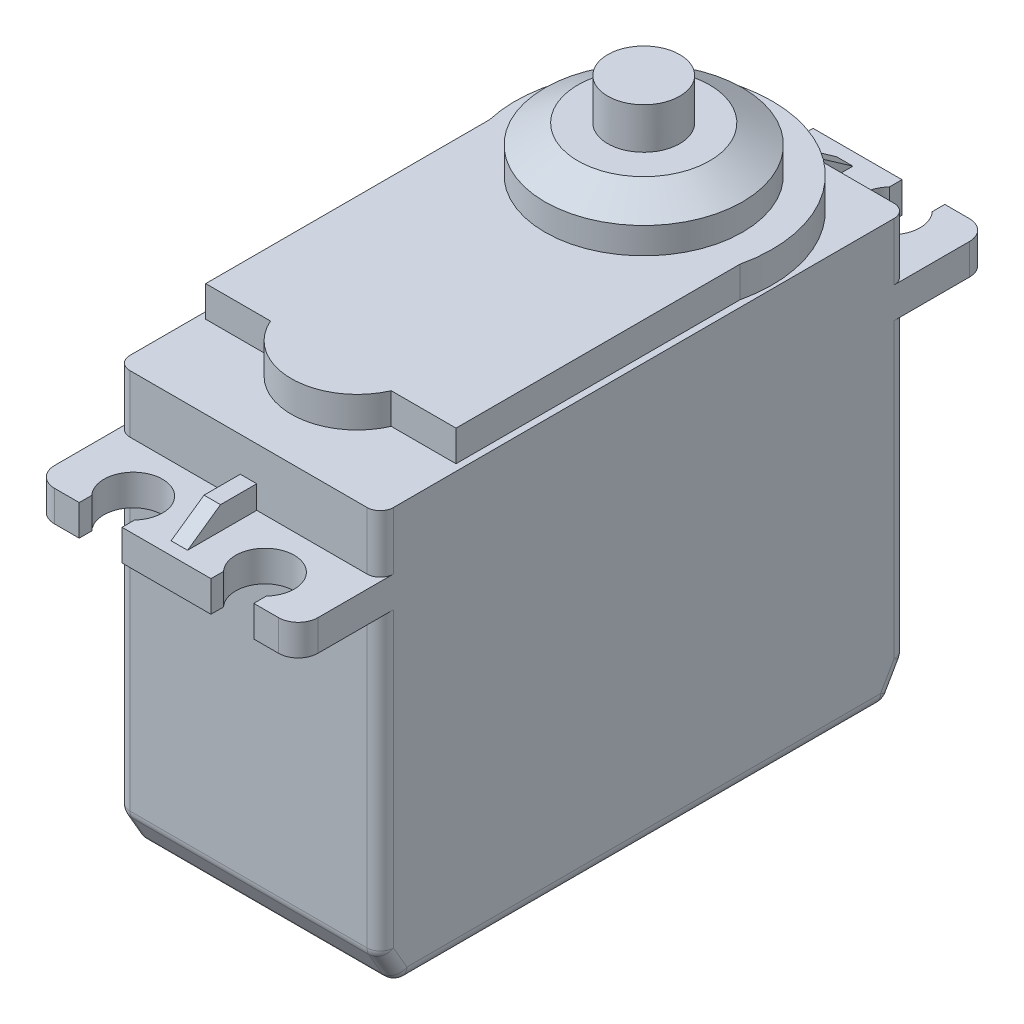
SolidWorks part; units mm, degrees
ref_plane "Front Plane" through (0, 0, 0) normal (0, 0, 1) x (1, 0, 0)
ref_plane "Top Plane" through (0, 0, 0) normal (0, 1, 0) x (1, 0, 0)
ref_plane "Right Plane" through (0, 0, 0) normal (1, 0, 0) x (0, 0, -1)
sketch "Sketch1" plane through (0, 0, 0) normal (0, 1, 0) x (1, 0, 0)
  line L1 (-10.16, 10.16) -> (10.16, 10.16)
  line L2 (-10.16, 10.16) -> (-10.16, -30.48)
  line L3 (-10.16, -30.48) -> (10.16, -30.48)
  line L4 (10.16, 10.16) -> (10.16, -30.48)
  dimension "D1" = 20.32
  dimension "D2" = 40.64
  dimension "D3" = 10.16
  dimension "D4" = 10.16
extrude "Extrude1" add sketch "Sketch1" along normal blind 25.4
sketch "Sketch2" plane through (0, 25.4, 0) normal (0, 1, 0) x (-1, 0, 0)
  line L0 (10.16, 30.48) -> (10.16, 36.8046)
  line L1 (10.16, 36.8046) -> (6.731, 36.8046)
  line L2 (-10.16, 36.8046) -> (-10.16, 30.48)
  line L3 (10.16, -10.16) -> (10.16, -16.4846)
  line L4 (10.16, -10.16) -> (10.16, 30.48)
  line L5 (10.16, 30.48) -> (-10.16, 30.48)
  line L6 (-10.16, 30.48) -> (-10.16, -10.16)
  line L7 (-10.16, -10.16) -> (10.16, -10.16)
  line L8 (10.16, -10.16) -> (10.16, 30.48)
  line L9 (10.16, 30.48) -> (-10.16, 30.48)
  line L10 (-10.16, 30.48) -> (-10.16, -10.16)
  line L11 (-10.16, -10.16) -> (10.16, -10.16)
  line L12 (10.16, -16.4846) -> (6.731, -16.4846)
  line L13 (-10.16, -16.4846) -> (-10.16, -10.16)
  line L14 (-6.731, 35.8342) -> (-6.731, 36.8046)
  line L15 (-3.429, 35.8342) -> (-3.429, 36.8046)
  line L16 (3.429, 35.8342) -> (3.429, 36.8046)
  line L17 (6.731, 35.8342) -> (6.731, 36.8046)
  line L18 (6.731, -15.5142) -> (6.731, -16.4846)
  line L19 (3.429, -15.5142) -> (3.429, -16.4846)
  line L20 (-3.429, -15.5142) -> (-3.429, -16.4846)
  line L21 (-6.731, -15.5142) -> (-6.731, -16.4846)
  line L22 (-6.731, -16.4846) -> (-10.16, -16.4846)
  line L23 (3.429, -16.4846) -> (-3.429, -16.4846)
  line L24 (-6.731, 36.8046) -> (-10.16, 36.8046)
  line L25 (3.429, 36.8046) -> (-3.429, 36.8046)
  arc A0 (3.429, 35.8342) -> (6.731, 35.8342) centre (5.08, 34.29) ccw
  arc A1 (-6.731, 35.8342) -> (-3.429, 35.8342) centre (-5.08, 34.29) ccw
  arc A2 (-3.429, -15.5142) -> (-6.731, -15.5142) centre (-5.08, -13.97) ccw
  arc A3 (6.731, -15.5142) -> (3.429, -15.5142) centre (5.08, -13.97) ccw
  line M5 (10.16, -10.16) -> (10.16, 30.48)
  line M6 (10.16, 30.48) -> (-10.16, 30.48)
  line M7 (-10.16, 30.48) -> (-10.16, -10.16)
  line M8 (-10.16, -10.16) -> (10.16, -10.16)
  dimension "D2" = 4.5212
  dimension "D9" = 3.302
  dimension "D3" = 5.08
  dimension "D4" = 10.16
  dimension "D5" = 48.26
  dimension "D6" = 3.81
  dimension "D7" = 6.3246
  dimension "D8" = 6.3246
  dimension "D10" = 3.302
  dimension "D11" = 1.651
  dimension "D12" = 1.651
  dimension "D1" = 0
extrude "Extrude2" add sketch "Sketch2" along normal blind 2.3813 contours M8 M5 M6 M7 | A3 L18 L12 L3 L13 L22 L21 A2 L20 L23 L19 M8 | A1 L14 L24 L2 L0 L1 L17 A0 L16 L25 L15 M6
sketch "Sketch3" plane through (0, 27.7812, 0) normal (0, 1, 0) x (-1, 0, 0)
  line L4 (10.16, -10.16) -> (10.16, 30.48)
  line L5 (-10.16, -10.16) -> (10.16, -10.16)
  line L6 (-10.16, 30.48) -> (-10.16, -10.16)
  line L7 (10.16, 30.48) -> (-10.16, 30.48)
  line L8 (10.16, -10.16) -> (10.16, 30.48)
  line L9 (-10.16, -10.16) -> (10.16, -10.16)
  line L10 (-10.16, 30.48) -> (-10.16, -10.16)
  line L11 (10.16, 30.48) -> (-10.16, 30.48)
  dimension "D1" = 0
extrude "Extrude3" add sketch "Sketch3" along normal blind 4.445
sketch "Sketch4" plane through (0, 32.2263, 0) normal (0, 1, 0) x (-1, 0, 0)
  line L0 (9.652, 2.2288) -> (9.652, 24.13)
  line L1 (9.652, 24.13) -> (4.6559, 24.13)
  line L2 (-9.652, 24.13) -> (-9.652, 2.2288)
  line L3 (10.16, 30.48) -> (-10.16, 30.48) construction
  line L4 (-4.6559, 24.13) -> (-9.652, 24.13)
  arc A0 (-9.652, 2.2288) -> (9.652, 2.2288) centre (0, 0) ccw
  arc A1 (4.6559, 24.13) -> (-4.6559, 24.13) centre (0, 22.098) ccw
  dimension "D1" = 19.812
  dimension "D5" = 5.08
  dimension "D2" = 6.35
  dimension "D3" = 19.304
  dimension "D4" = 9.652
  dimension "D6" = 2.032
extrude "Extrude4" add sketch "Sketch4" along normal blind 2.3813
ref_plane "Plane1" through (0, 38.1, 0) normal (0, -1, 0) x (1, 0, 0)
sketch "Sketch5" plane through (0, 34.6075, 0) normal (0, 1, 0) x (-1, 0, 0)
  circle A0 centre (0, 0) radius 7.62
  dimension "D1" = 15.24
extrude "Extrude5" add sketch "Sketch5" along normal up to surface (3.4925 mm away) up to plane "Plane1"
chamfer "Chamfer1" distance 2.54 angle 30 1 edges at (0, 38.1, -7.62)
sketch "Sketch7" plane through (0, 0, 0) normal (1, 0, 0) x (0, 0, -1)
  line L0 (15.494, 27.7812) -> (12.954, 29.5592)
  line L4 (12.954, 29.5592) -> (10.16, 29.5592)
  line L5 (10.16, 32.2263) -> (10.16, 27.7812) construction
  line L6 (16.4846, 27.7812) -> (10.16, 27.7812) construction
  line L7 (10.16, 29.5592) -> (10.16, 27.7812)
  line L8 (10.16, 27.7812) -> (15.494, 27.7812)
  dimension "D1" = 1.778
  dimension "D2" = 2.794
  dimension "D3" = 5.334
extrude "Extrude6" add sketch "Sketch7" along normal mid plane 1.27
ref_plane "Plane2" through (0, 0, 10.16) normal (0, 0, -1) x (-1, 0, 0)
mirror "Mirror1" about plane through (0, 0, 10.16) normal (0, 0, -1) of "Extrude6"
sketch "Sketch8" plane through (0, 38.1, 0) normal (0, 1, 0) x (-1, 0, 0)
  circle A0 centre (0, 0) radius 2.7781
  dimension "D1" = 5.5562
extrude "Extrude7" add sketch "Sketch8" along normal blind 3.175
chamfer "Chamfer2" distance 2.54 angle 30 2 edges at (0, 0, 30.48) (0, 0, -10.16)
fillet "Fillet1" radius 1.016 18 edges at (10.16, 0, 10.16) (10.16, 1.27, -9.4268) (0, 0, -8.6935) (0, 2.54, -10.16) (-10.16, 1.27, -9.4268) (10.16, 1.27, 29.7468) (0, 2.54, 30.48) (-10.16, 0, 10.16) (0, 0, 29.0135) (-10.16, 1.27, 29.7468)
fillet "Fillet2" radius 1.524 4 edges at (-10.16, 26.5906, 36.8046) (10.16, 26.5906, 36.8046) (-10.16, 26.5906, -16.4846) (10.16, 26.5906, -16.4846)
sketch "Sketch9" plane through (0, 0, -10.16) normal (0, 0, -1) x (-1, 0, 0)
  line L1 (-3.175, 5.588) -> (3.175, 5.588)
  line L2 (-3.175, 5.588) -> (-3.175, 3.048)
  line L3 (-3.175, 3.048) -> (3.175, 3.048)
  line L4 (3.175, 5.588) -> (3.175, 3.048)
  dimension "D1" = 6.35
  dimension "D2" = 2.54
  dimension "D3" = 3.048
  dimension "D4" = 3.175
extrude "Extrude8" add sketch "Sketch9" along normal blind 2.3813
sketch "Sketch10" plane through (0, 0, -12.5412) normal (0, 0, -1) x (-1, 0, 0)
  line L8 (-2.54, 4.953) -> (-2.54, 3.683)
  line L9 (-2.54, 3.683) -> (2.54, 3.683)
  line L10 (2.54, 3.683) -> (2.54, 4.953)
  line L11 (2.54, 4.953) -> (-2.54, 4.953)
  line L12 (-2.54, 4.953) -> (-2.54, 3.683)
  line L13 (-2.54, 3.683) -> (2.54, 3.683)
  line L14 (2.54, 3.683) -> (2.54, 4.953)
  line L15 (2.54, 4.953) -> (-2.54, 4.953)
  dimension "D1" = 0.635
extrude "Cut-Extrude1" cut sketch "Sketch10" against normal up to surface (2.3813 mm away) up to face at (2.286, 14.1061, -10.16)
